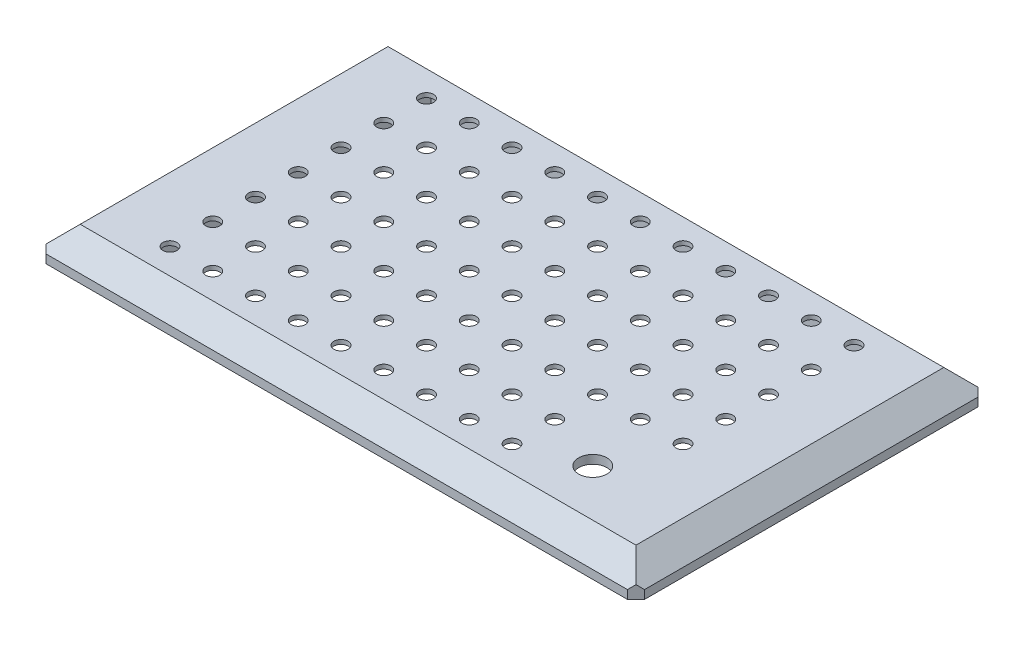
SolidWorks part; units mm, degrees
ref_plane "Front Plane" through (0, 0, 0) normal (0, 0, 1) x (1, 0, 0)
ref_plane "Top Plane" through (0, 0, 0) normal (0, 1, 0) x (1, 0, 0)
ref_plane "Right Plane" through (0, 0, 0) normal (1, 0, 0) x (0, 0, -1)
sketch "Sketch1" plane through (0, 0, 0) normal (0, 1, 0) x (1, 0, 0)
  line L1 (-70, -41) -> (70, -41)
  line L2 (-70, -41) -> (-70, 41)
  line L3 (-70, 41) -> (70, 41)
  line L4 (70, -41) -> (70, 41)
  line L5 (-70, -41) -> (70, 41) construction
  line L6 (-70, 41) -> (70, -41) construction
  point P0 (0, 0)
  dimension "D1" = 140
  dimension "D2" = 82
extrude "Boss-Extrude1" add sketch "Sketch1" along normal blind 2
sketch "Sketch2" plane through (0, 2, 0) normal (0, 1, 0) x (1, 0, 0)
  line L4 (70, -41) -> (70, 41)
  line L5 (70, 41) -> (-70, 41)
  line L6 (-70, 41) -> (-70, -41)
  line L7 (-70, -41) -> (70, -41)
  line L8 (70, -41) -> (70, 41)
  line L9 (70, 41) -> (-70, 41)
  line L10 (-70, 41) -> (-70, -41)
  line L11 (-70, -41) -> (70, -41)
  dimension "D1" = 0
ref_plane "Plane1" through (0, 7, 0) normal (0, 1, 0) x (1, 0, 0)
sketch "Sketch3" plane through (0, 7, 0) normal (0, 1, 0) x (1, 0, 0)
  line L0 (-70, 41) -> (-70, -41) construction
  line L1 (-65, -36) -> (65, -36)
  line L2 (-65, -36) -> (-65, 36)
  line L3 (-65, 36) -> (65, 36)
  line L4 (65, -36) -> (65, 36)
  line L5 (-65, -36) -> (65, 36) construction
  line L6 (-65, 36) -> (65, -36) construction
  line L7 (70, 41) -> (-70, 41) construction
  point P0 (0, 0)
  dimension "D1" = 5
  dimension "D2" = 5
loft "Loft1" add profiles "Sketch3", "Sketch2"
chamfer "Chamfer2" distance 2 angle 45 4 edges at (70, 1, 41) (70, 1, -41) (-70, 1, -41) (-70, 1, 41)
sketch "Sketch4" plane through (0, 0, 0) normal (0, -1, 0) x (1, 0, 0)
  line L0 (-70, -39) -> (-70, 39) construction
  line L1 (-62.9, 15) -> (-54.9, 15)
  line L2 (-62.9, 15) -> (-62.9, 25)
  line L3 (-62.9, 25) -> (-54.9, 25)
  line L4 (-54.9, 15) -> (-54.9, 25)
  line L5 (-62.9, 15) -> (-54.9, 25) construction
  line L6 (-62.9, 25) -> (-54.9, 15) construction
  line L7 (-70, 0) -> (70, 0) construction
  line L8 (70, 39) -> (70, -39) construction
  line L9 (0, 41) -> (0, -41) construction
  line L10 (-68, 41) -> (68, 41) construction
  line L11 (68, -41) -> (-68, -41) construction
  line L12 (-62.9, -25) -> (-54.9, -15) construction
  line L13 (-62.9, -15) -> (-54.9, -25) construction
  line L14 (-54.9, -15) -> (-54.9, -25)
  line L15 (-62.9, -25) -> (-54.9, -25)
  line L16 (-62.9, -15) -> (-62.9, -25)
  line L17 (-62.9, -15) -> (-54.9, -15)
  line L18 (62.9, -15) -> (54.9, -25) construction
  line L19 (62.9, -25) -> (54.9, -15) construction
  line L20 (62.9, 25) -> (54.9, 15) construction
  line L21 (62.9, 15) -> (54.9, 25) construction
  line L22 (62.9, -15) -> (54.9, -15)
  line L23 (62.9, -15) -> (62.9, -25)
  line L24 (62.9, -25) -> (54.9, -25)
  line L25 (54.9, -15) -> (54.9, -25)
  line L26 (54.9, 15) -> (54.9, 25)
  line L27 (62.9, 25) -> (54.9, 25)
  line L28 (62.9, 15) -> (62.9, 25)
  line L29 (62.9, 15) -> (54.9, 15)
  point P0 (-58.9, 20)
  point P21 (-58.9, -20)
  point P30 (58.9, -20)
  point P31 (58.9, 20)
  dimension "D1" = 10
  dimension "D2" = 7.1
  dimension "D3" = 8
  dimension "D4" = 40
extrude "Boss-Extrude2" add sketch "Sketch4" along normal blind 7
sketch "Sketch5" plane through (-62.9, 0, 0) normal (-1, 0, 0) x (0, 0, 1)
  line L0 (-15, 0) -> (-25, -7) construction
  line L1 (0, 0) -> (0, 50000) construction
  circle A0 centre (-20, -3.5) radius 2.05
  circle A1 centre (20, -3.5) radius 2.05
  dimension "D1" = 4.1
extrude "Cut-Extrude1" cut sketch "Sketch5" against normal through all
sketch "Sketch6" plane through (0, 0, 0) normal (0, -1, 0) x (1, 0, 0)
  line L0 (54.9, 25) -> (54.9, 15) construction
  line L1 (-53.9, -35) -> (53.9, -35)
  line L2 (-53.9, -35) -> (-53.9, 35)
  line L3 (-53.9, 35) -> (53.9, 35)
  line L4 (53.9, -35) -> (53.9, 35)
  line L5 (-53.9, -35) -> (53.9, 35) construction
  line L6 (-53.9, 35) -> (53.9, -35) construction
  line L8 (-65, 36) -> (65, 36) construction
  point P0 (0, 0)
  dimension "D1" = 1
  dimension "D2" = 1
extrude "Cut-Extrude2" cut sketch "Sketch6" against normal offset from surface (5 mm away) 2 up to face at (0, 7, 0)
sketch "Sketch7" plane through (0, 5, 0) normal (0, -1, 0) x (1, 0, 0)
  line L0 (0, 35) -> (0, -35) construction
  line L1 (-53.9, 35) -> (53.9, 35) construction
  line L2 (-53.9, -35) -> (53.9, -35) construction
  line L3 (-53.9, 0) -> (53.9, 0) construction
  line L4 (-53.9, -35) -> (-53.9, 35) construction
  line L5 (53.9, 35) -> (53.9, -35) construction
  circle A0 centre (0, 0) radius 1.65
  circle A1 centre (10, 0) radius 1.65
  circle A2 centre (20, 0) radius 1.65
  circle A3 centre (30, 0) radius 1.65
  circle A4 centre (40, 0) radius 1.65
  circle A5 centre (50, 0) radius 1.65
  circle A7 centre (10, 10) radius 1.65
  circle A8 centre (20, 10) radius 1.65
  circle A9 centre (30, 10) radius 1.65
  circle A10 centre (40, 10) radius 1.65
  circle A11 centre (50, 10) radius 1.65
  circle A13 centre (10, 20) radius 1.65
  circle A14 centre (20, 20) radius 1.65
  circle A15 centre (30, 20) radius 1.65
  circle A16 centre (40, 20) radius 1.65
  circle A17 centre (50, 20) radius 1.65
  circle A19 centre (10, 30) radius 1.65
  circle A20 centre (20, 30) radius 1.65
  circle A21 centre (30, 30) radius 1.65
  circle A22 centre (40, 30) radius 1.65
  circle A23 centre (50, 30) radius 1.65
  circle A25 centre (0, 10) radius 1.65
  circle A26 centre (0, 20) radius 1.65
  circle A27 centre (0, 30) radius 1.65
  circle A35 centre (-50, 30) radius 1.65
  circle A36 centre (-40, 30) radius 1.65
  circle A37 centre (-30, 30) radius 1.65
  circle A38 centre (-20, 30) radius 1.65
  circle A39 centre (-10, 30) radius 1.65
  circle A40 centre (-50, 20) radius 1.65
  circle A41 centre (-40, 20) radius 1.65
  circle A42 centre (-30, 20) radius 1.65
  circle A43 centre (-20, 20) radius 1.65
  circle A44 centre (-10, 20) radius 1.65
  circle A45 centre (-50, 10) radius 1.65
  circle A46 centre (-40, 10) radius 1.65
  circle A47 centre (-30, 10) radius 1.65
  circle A48 centre (-20, 10) radius 1.65
  circle A49 centre (-10, 10) radius 1.65
  circle A50 centre (-50, 0) radius 1.65
  circle A51 centre (-40, 0) radius 1.65
  circle A52 centre (-30, 0) radius 1.65
  circle A53 centre (-20, 0) radius 1.65
  circle A54 centre (-10, 0) radius 1.65
  circle A55 centre (-10, -10) radius 1.65
  circle A56 centre (-20, -10) radius 1.65
  circle A57 centre (-30, -10) radius 1.65
  circle A58 centre (-40, -10) radius 1.65
  circle A59 centre (-50, -10) radius 1.65
  circle A60 centre (-10, -20) radius 1.65
  circle A61 centre (-20, -20) radius 1.65
  circle A62 centre (-30, -20) radius 1.65
  circle A63 centre (-40, -20) radius 1.65
  circle A64 centre (-50, -20) radius 1.65
  circle A65 centre (-10, -30) radius 1.65
  circle A66 centre (-20, -30) radius 1.65
  circle A67 centre (-30, -30) radius 1.65
  circle A68 centre (-40, -30) radius 1.65
  circle A69 centre (-50, -30) radius 1.65
  circle A70 centre (0, -30) radius 1.65
  circle A71 centre (0, -20) radius 1.65
  circle A72 centre (0, -10) radius 1.65
  circle A73 centre (50, -30) radius 1.65
  circle A74 centre (40, -30) radius 1.65
  circle A75 centre (30, -30) radius 1.65
  circle A76 centre (20, -30) radius 1.65
  circle A77 centre (10, -30) radius 1.65
  circle A78 centre (50, -20) radius 1.65
  circle A79 centre (40, -20) radius 1.65
  circle A80 centre (30, -20) radius 1.65
  circle A81 centre (20, -20) radius 1.65
  circle A82 centre (10, -20) radius 1.65
  circle A83 centre (50, -10) radius 1.65
  circle A84 centre (40, -10) radius 1.65
  circle A85 centre (30, -10) radius 1.65
  circle A86 centre (20, -10) radius 1.65
  circle A87 centre (10, -10) radius 1.65
  dimension "D1" = 3.3
  dimension "D2" = 6
  dimension "D3" = 4
extrude "Cut-Extrude3" cut sketch "Sketch7" against normal through all
sketch "Sketch8" plane through (0, 5, 0) normal (0, -1, 0) x (1, 0, 0)
  line L0 (0, 35) -> (0, -35) construction
  line L1 (-53.9, 35) -> (53.9, 35) construction
  line L2 (53.9, -35) -> (-53.9, -35) construction
  line L3 (-53.9, 0) -> (53.9, 0) construction
  line L4 (-53.9, -35) -> (-53.9, 35) construction
  line L5 (53.9, -35) -> (53.9, 35) construction
  circle A0 centre (0, 0) radius 3.25
  circle A1 centre (10, 0) radius 3.25
  circle A2 centre (20, 0) radius 3.25
  circle A3 centre (30, 0) radius 3.25
  circle A4 centre (40, 0) radius 3.25
  circle A5 centre (50, 0) radius 3.25
  circle A6 centre (10, 10) radius 3.25
  circle A7 centre (20, 10) radius 3.25
  circle A8 centre (30, 10) radius 3.25
  circle A9 centre (40, 10) radius 3.25
  circle A10 centre (50, 10) radius 3.25
  circle A11 centre (10, 20) radius 3.25
  circle A12 centre (20, 20) radius 3.25
  circle A13 centre (30, 20) radius 3.25
  circle A14 centre (40, 20) radius 3.25
  circle A15 centre (50, 20) radius 3.25
  circle A16 centre (10, 30) radius 3.25
  circle A17 centre (20, 30) radius 3.25
  circle A18 centre (30, 30) radius 3.25
  circle A19 centre (40, 30) radius 3.25
  circle A20 centre (50, 30) radius 3.25
  circle A21 centre (0, 10) radius 3.25
  circle A22 centre (0, 20) radius 3.25
  circle A23 centre (0, 30) radius 3.25
  circle A24 centre (0, -30) radius 3.25
  circle A25 centre (0, -20) radius 3.25
  circle A26 centre (0, -10) radius 3.25
  circle A27 centre (50, -30) radius 3.25
  circle A28 centre (40, -30) radius 3.25
  circle A29 centre (30, -30) radius 3.25
  circle A30 centre (20, -30) radius 3.25
  circle A31 centre (10, -30) radius 3.25
  circle A32 centre (50, -20) radius 3.25
  circle A33 centre (40, -20) radius 3.25
  circle A34 centre (30, -20) radius 3.25
  circle A35 centre (20, -20) radius 3.25
  circle A36 centre (10, -20) radius 3.25
  circle A37 centre (50, -10) radius 3.25
  circle A38 centre (40, -10) radius 3.25
  circle A39 centre (30, -10) radius 3.25
  circle A40 centre (20, -10) radius 3.25
  circle A41 centre (10, -10) radius 3.25
  circle A42 centre (-10, -10) radius 3.25
  circle A43 centre (-20, -10) radius 3.25
  circle A44 centre (-30, -10) radius 3.25
  circle A45 centre (-40, -10) radius 3.25
  circle A46 centre (-50, -10) radius 3.25
  circle A47 centre (-10, -20) radius 3.25
  circle A48 centre (-20, -20) radius 3.25
  circle A49 centre (-30, -20) radius 3.25
  circle A50 centre (-40, -20) radius 3.25
  circle A51 centre (-50, -20) radius 3.25
  circle A52 centre (-10, -30) radius 3.25
  circle A53 centre (-20, -30) radius 3.25
  circle A54 centre (-30, -30) radius 3.25
  circle A55 centre (-40, -30) radius 3.25
  circle A56 centre (-50, -30) radius 3.25
  circle A57 centre (-50, 30) radius 3.25
  circle A58 centre (-40, 30) radius 3.25
  circle A59 centre (-30, 30) radius 3.25
  circle A60 centre (-20, 30) radius 3.25
  circle A61 centre (-10, 30) radius 3.25
  circle A62 centre (-50, 20) radius 3.25
  circle A63 centre (-40, 20) radius 3.25
  circle A64 centre (-30, 20) radius 3.25
  circle A65 centre (-20, 20) radius 3.25
  circle A66 centre (-10, 20) radius 3.25
  circle A67 centre (-50, 10) radius 3.25
  circle A68 centre (-40, 10) radius 3.25
  circle A69 centre (-30, 10) radius 3.25
  circle A70 centre (-20, 10) radius 3.25
  circle A71 centre (-10, 10) radius 3.25
  circle A72 centre (-50, 0) radius 3.25
  circle A73 centre (-40, 0) radius 3.25
  circle A74 centre (-30, 0) radius 3.25
  circle A75 centre (-20, 0) radius 3.25
  circle A76 centre (-10, 0) radius 3.25
  dimension "D1" = 6.5
  dimension "D2" = 6
  dimension "D3" = 4
extrude "Cut-Extrude4" cut sketch "Sketch8" against normal blind 1
sketch "Sketch9" plane through (0, 7, 0) normal (0, 1, 0) x (1, 0, 0)
  line L1 (53.9, -35) -> (33.9, -35)
  line L2 (53.9, -35) -> (53.9, -15)
  line L3 (53.9, -15) -> (33.9, -15)
  line L4 (33.9, -35) -> (33.9, -15)
  dimension "D1" = 20
  dimension "D2" = 20
extrude "Boss-Extrude3" add sketch "Sketch9" against normal up to surface (2 mm away) up to face at (10, 5, -6.75)
sketch "Sketch10" plane through (0, 5, 0) normal (0, -1, 0) x (1, 0, 0)
  line L1 (53.9, 35) -> (43.9, 35) construction
  line L2 (53.9, 35) -> (53.9, 25) construction
  line L3 (53.9, 25) -> (43.9, 25) construction
  line L4 (43.9, 35) -> (43.9, 25) construction
  circle A0 centre (43.9, 25) radius 3.3
  dimension "D1" = 6.6
  dimension "D2" = 10
extrude "Cut-Extrude5" cut sketch "Sketch10" against normal through all
